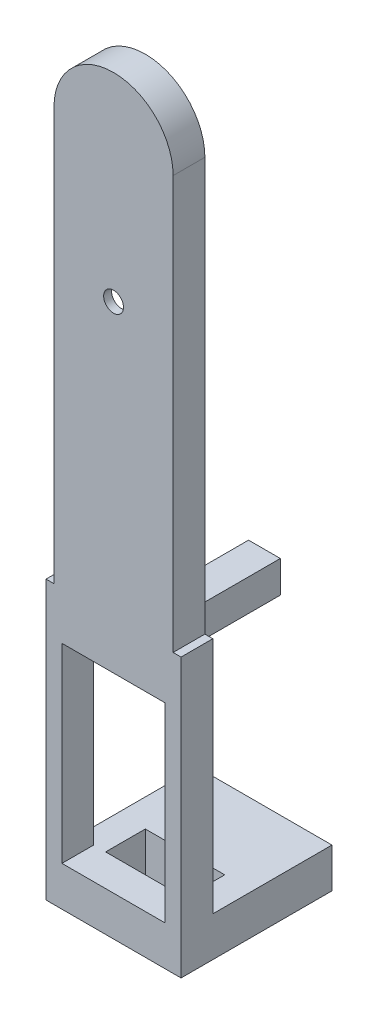
SolidWorks part; units mm, degrees
ref_plane "前基準面" through (0, 0, 0) normal (0, 0, 1) x (1, 0, 0)
ref_plane "上基準面" through (0, 0, 0) normal (0, 1, 0) x (1, 0, 0)
ref_plane "右基準面" through (0, 0, 0) normal (1, 0, 0) x (0, 0, -1)
sketch "草圖1" plane through (0, 0, 0) normal (0, 0, 1) x (1, 0, 0)
  line L0 (0, 0) -> (0, 4.6483) construction
  line L1 (7.5, 0) -> (7.5, 52)
  line L2 (7.5, 0) -> (-7.5, 0)
  line L3 (-7.5, 0) -> (-7.5, 52)
  arc A0 (7.5, 52) -> (-7.5, 52) centre (0, 52) ccw
  dimension "D1" = 7.5
  dimension "D2" = 52
extrude "填料-伸長1" add sketch "草圖1" along normal blind 4
sketch "草圖3" plane through (0, 0, 0) normal (0, 0, 1) x (1, 0, 0)
  line L0 (0, 0) -> (0, 14.8578) construction
  line L1 (7.5, 52) -> (-7.5, 52) construction
  line L2 (7.5, 15) -> (-7.5, 15) construction
  line L3 (7.5, 0) -> (7.5, 52) construction
  line L4 (-7.5, 52) -> (-7.5, 0) construction
  line L6 (7.5, 34.5) -> (5, 34.5) construction
  line L7 (5, 34.5) -> (2.1147, 16.658)
  line L8 (5, 34.5) -> (2.1328, 52)
  line L9 (-2.1328, 52) -> (-5, 34.5)
  line L10 (-5, 34.5) -> (-2.1422, 17)
  line L11 (0, 54.1328) -> (0, 59.5) construction
  line L12 (-5, 34.5) -> (-7.5, 34.5) construction
  arc A0 (7.5, 52) -> (-7.5, 52) centre (0, 52) ccw construction
  arc A1 (-4.7386, 36.0956) -> (-4.7403, 32.9094) centre (0, 34.5) ccw
  arc A2 (-2.1422, 17) -> (2.1147, 16.658) centre (0, 17) ccw
  arc A3 (-2.1328, 52) -> (2.1328, 52) centre (0, 52) cw
  arc A4 (4.7452, 32.9241) -> (4.7386, 36.0956) centre (0, 34.5) ccw
  dimension "D4" = 10
  dimension "D1" = 35
extrude "除料-伸長1" cut sketch "草圖3" along normal blind 3 contours A3 L9 L10 A2 L7 L8
sketch "草圖5" plane through (0, 0, 0) normal (0, 0, 1) x (1, 0, 0)
  line L0 (5, 34.5) -> (-5, 34.5) construction
  circle A0 centre (0, 34.5) radius 1.25
  dimension "D1" = 2.5
extrude "除料-伸長2" cut sketch "草圖5" along normal blind 12.4
sketch "草圖6" plane through (0, 0, 0) normal (0, 0, 1) x (1, 0, 0)
  line L0 (0, 62.3953) -> (0, -4.428) construction
  line L1 (0, -2.2) -> (0, 2.2) construction
  line L3 (8.5, 0) -> (-8.5, 0)
  line L4 (8.5, 0) -> (8.5, -35)
  line L5 (8.5, -35) -> (-8.5, -35)
  line L6 (-8.5, 0) -> (-8.5, -35)
  dimension "D1" = 17
  dimension "D2" = 8.5
  dimension "D3" = 35
extrude "填料-伸長2" add sketch "草圖6" along normal blind 4
sketch "草圖7" plane through (0, 0, 0) normal (0, 0, 1) x (1, 0, 0)
  line L0 (0, 64.1958) -> (0, -38.5274) construction
  line L1 (0, -36.025) -> (0, 36.025) construction
  line L3 (-6.5, -6) -> (6.5, -6)
  line L4 (-6.5, -6) -> (-6.5, -30)
  line L5 (-6.5, -30) -> (6.5, -30)
  line L6 (6.5, -6) -> (6.5, -30)
  line L7 (-8.5, -35) -> (8.5, -35) construction
  dimension "D1" = 6.5
  dimension "D2" = 13
  dimension "D3" = 24
  dimension "D4" = 5
extrude "除料-伸長3" cut sketch "草圖7" along normal blind 12.1
sketch "草圖8" plane through (0, 0, 0) normal (0, 0, 1) x (1, 0, 0)
  line L0 (0, 64.1958) -> (0, -34.8274) construction
  line L1 (0, -36.025) -> (0, 36.025) construction
  line L2 (0, 64.1958) -> (0, -39.0142) construction
  line L3 (6.5, -18) -> (-6.5, -18) construction
  line L4 (6.5, -30) -> (6.5, -6) construction
  line L5 (-6.5, -6) -> (-6.5, -30) construction
  line L6 (6.5, -6) -> (-6.5, -6) construction
  line L7 (2, -2) -> (-2, -2)
  line L8 (2, -2) -> (2, -6)
  line L9 (2, -6) -> (-2, -6)
  line L10 (-2, -2) -> (-2, -6)
  circle A0 centre (0, -4) radius 1.175
  dimension "D5" = 2.35
  dimension "D1" = 4
  dimension "D2" = 4
  dimension "D3" = 2
  dimension "D4" = 2
extrude "填料-伸長3" add sketch "草圖8" against normal blind 15
ref_plane "平面1" through (0, -35, 0) normal (0, 1, 0) x (1, 0, 0)
sketch "草圖9" plane through (0, -35, 0) normal (0, 1, 0) x (1, 0, 0)
  line L0 (0, 15.9246) -> (0, -4.8463) construction
  line L1 (0, -36.025) -> (0, 36.025) construction
  line L2 (-5, 0) -> (-5, 5)
  line L3 (7.5, 0) -> (-7.5, 0) construction
  line L4 (-5, 5) -> (5, 5)
  line L5 (-5, 0) -> (5, 0)
  line L6 (5, 0) -> (5, 5)
  line L12 (-8.5, 0) -> (8.5, 0)
  line L16 (8.5, 0) -> (8.5, 15)
  line L17 (8.5, 15) -> (-8.5, 15)
  line L19 (-8.5, 15) -> (-8.5, 0)
  point P12 (0, 0)
  point P13 (0, 5)
  point P20 (0, 0)
  point P21 (0, 15)
  point P25 (0, 0)
  point P26 (0, 15)
  dimension "D1" = 5
  dimension "D2" = 5
  dimension "D3" = 5
extrude "填料-伸長4" add sketch "草圖9" along normal blind 5
sketch "草圖10" plane through (0, 0, -15) normal (0, 0, -1) x (-1, 0, 0)
  line L0 (0, 0) -> (0, -35) construction
  line L1 (8.5, -35) -> (-8.5, -35) construction
  line L5 (8.538, -32.5) -> (-8.538, -32.5) construction
  circle A0 centre (0, -32.5) radius 1.175
  dimension "D2" = 2.35
  dimension "D1" = 2.5
extrude "除料-伸長4" cut sketch "草圖10" against normal blind 12.7 contours A0
